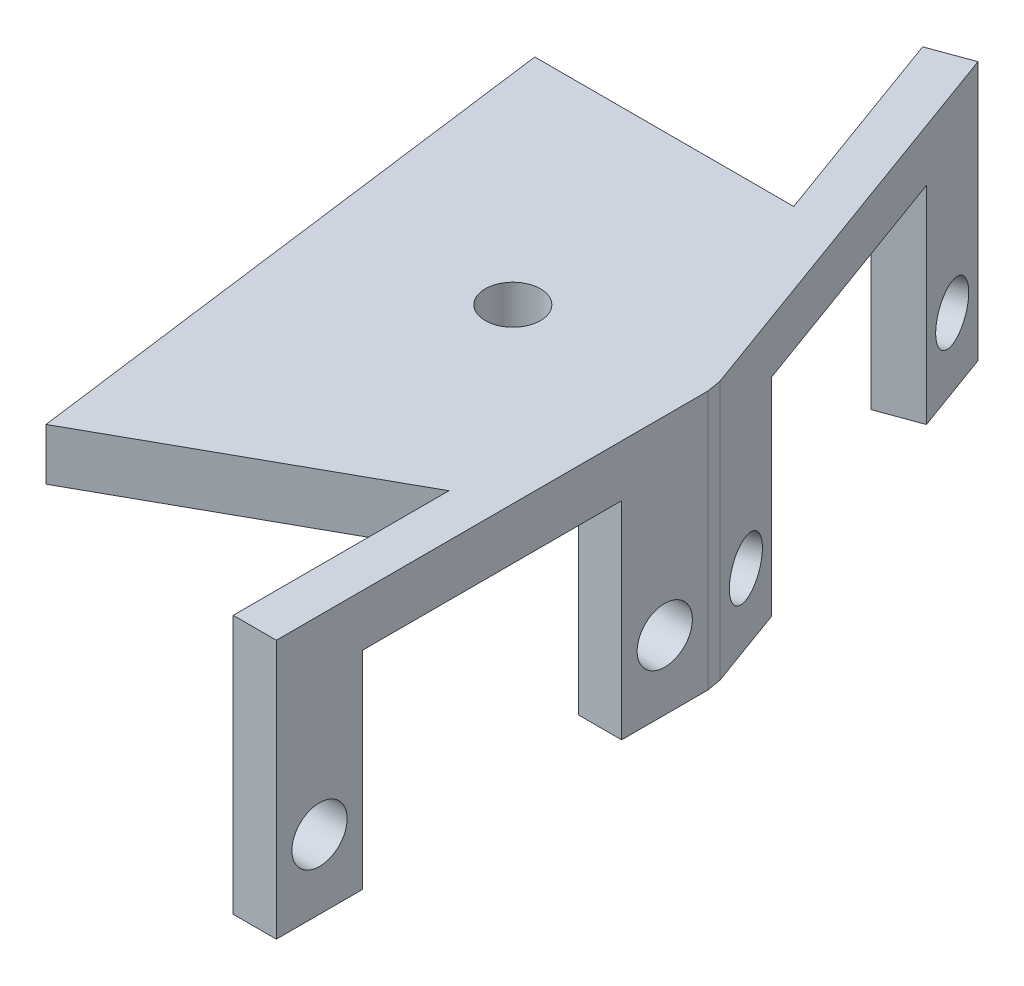
SolidWorks part; units mm, degrees
ref_plane "Front Plane" through (0, 0, 0) normal (0, 0, 1) x (1, 0, 0)
ref_plane "Top Plane" through (0, 0, 0) normal (0, 1, 0) x (1, 0, 0)
ref_plane "Right Plane" through (0, 0, 0) normal (1, 0, 0) x (0, 0, -1)
sketch "Sketch1" plane through (0, 0, 0) normal (0, 1, 0) x (1, 0, 0)
  line L0 (-2.9698, -0.171) -> (41.6122, -0.171) construction
  line L20 (-0.4698, -0.171) -> (-0.4698, -25.171)
  line L21 (-0.4698, -25.171) -> (-2.9698, -25.171)
  line L22 (-2.9698, -0.171) -> (-2.9698, -25.171)
  line L23 (-0.4698, -12.671) -> (36.346, -12.671) construction
  line L24 (-2.9698, -0.171) -> (38.229, 14.8242) construction
  line L26 (-2.9698, -0.171) -> (-11.5203, 23.3213)
  line L27 (-0.6206, 0.684) -> (-9.1711, 24.1764)
  line L28 (-11.5203, 23.3213) -> (-9.1711, 24.1764)
  line L29 (-4.8959, 12.4302) -> (41.2139, 29.2128) construction
  line L30 (-0.6206, 0.684) -> (-0.4698, -0.171)
  dimension "D1" = 20
  dimension "D2" = 25
  dimension "D3" = 25
  dimension "D4" = 2.5
  dimension "D5" = 2.5
extrude "Boss-Extrude1" add sketch "Sketch1" against normal blind 15
sketch "Sketch5" plane through (-0.4698, 0, 0) normal (1, 0, 0) x (0, 0, -1)
  line L0 (-0.171, -15) -> (-25.171, -15) construction
  line L1 (-20.171, -15) -> (-5.171, -15)
  line L2 (-20.171, -15) -> (-20.171, -3)
  line L3 (-20.171, -3) -> (-5.171, -3)
  line L4 (-5.171, -15) -> (-5.171, -3)
  line L9 (-0.171, 0) -> (-25.171, 0) construction
  line L10 (-25.171, -15) -> (-25.171, 0) construction
  circle A0 centre (-22.671, -11) radius 1.6
  circle A1 centre (-2.671, -11) radius 1.6
  dimension "D5" = 3.2
  dimension "D6" = 3.2
  dimension "D1" = 5
  dimension "D3" = 3
  dimension "D4" = 20
  dimension "D8" = 4
  dimension "2.55" = 2.5
sketch "Sketch6" plane through (0, 0, 0) normal (0, 1, 0) x (1, 0, 0)
  line L0 (-7.2451, 11.5751) -> (-22.2451, 11.5751)
  line L1 (-2.9698, -0.171) -> (-11.5203, 23.3213) construction
  line L2 (-22.2451, 11.5751) -> (-17.9698, -21.0165)
  line L3 (-17.9698, -21.0165) -> (-2.9698, -12.671)
  line L4 (-2.9698, -0.171) -> (-2.9698, -25.171) construction
  line L5 (-2.9698, -12.671) -> (-0.4698, -0.171)
  line L6 (-0.4698, -0.171) -> (-0.6206, 0.684)
  line L7 (-0.6206, 0.684) -> (-7.2451, 11.5751)
  line L8 (-0.5452, 0.2565) -> (-20.3034, -3.2274) construction
  circle A0 centre (-10.4523, -1.4904) radius 1.6
  dimension "D4" = 3.2
  dimension "D1" = 15
  dimension "D2" = 15
  dimension "D3" = 32.8709
sketch "Sketch8" plane through (-0.3282, 0, 0.1194) normal (0.9397, 0, -0.342) x (-0.342, 0, -0.9397)
  line L2 (5.8551, -15.1192) -> (20.8551, -15.1192)
  line L3 (5.8551, -15.1192) -> (5.8551, -3)
  line L4 (5.8551, -3) -> (20.8551, -3)
  line L5 (20.8551, -15.1192) -> (20.8551, -3)
  line L6 (0.8551, 0) -> (25.8551, 0) construction
  line L7 (0.8551, -15) -> (25.8551, -15) construction
  circle A0 centre (3.3551, -11) radius 1.6
  circle A1 centre (23.3551, -11) radius 1.6
  point P14 (0, 0)
  dimension "D4" = 3.2
  dimension "D2" = 15
  dimension "D3" = 3
  dimension "D5" = 2.5
  dimension "D6" = 20
  dimension "D7" = 4
extrude "Cut-Extrude4" cut sketch "Sketch5" against normal blind 15
extrude "Cut-Extrude5" cut sketch "Sketch8" against normal blind 15
extrude "Boss-Extrude8" add sketch "Sketch6" against normal blind 3
